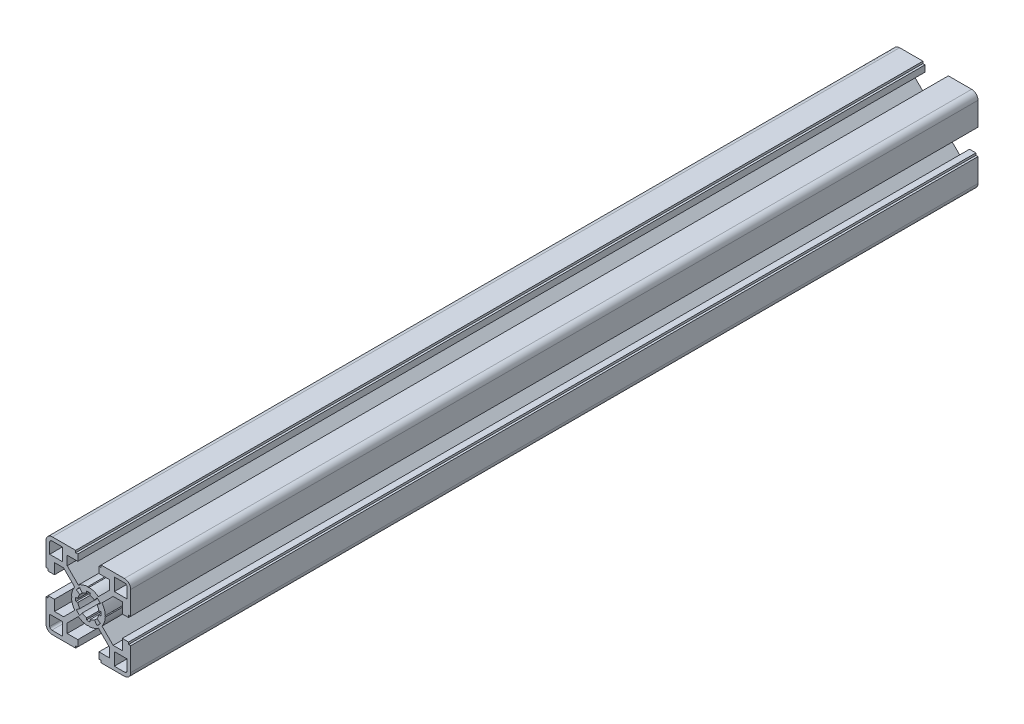
SolidWorks part; units mm, degrees
ref_plane "Plan de face" through (0, 0, 0) normal (0, 0, 1) x (1, 0, 0)
ref_plane "Plan de dessus" through (0, 0, 0) normal (0, 1, 0) x (1, 0, 0)
ref_plane "Plan de droite" through (0, 0, 0) normal (1, 0, 0) x (0, 0, -1)
ref_plane "Plan1" through (0, 0, 100) normal (0, 0, 1) x (1, 0, 0)
sketch "Esquisse1" plane through (0, 0, 100) normal (0, 0, 1) x (1, 0, 0)
  line L0 (18.25, 12.25) -> (12.25, 12.25)
  line L1 (12.25, 12.25) -> (12.25, 18.25)
  line L2 (12.25, 18.25) -> (17.25, 18.25)
  line L3 (18.25, 17.25) -> (18.25, 12.25)
  line L4 (-18.25, -12.25) -> (-12.25, -12.25)
  line L5 (-12.25, -12.25) -> (-12.25, -18.25)
  line L6 (-12.25, -18.25) -> (-17.25, -18.25)
  line L7 (-18.25, -17.25) -> (-18.25, -12.25)
  line L8 (6, -19) -> (6, -20)
  line L9 (6, -20) -> (17, -20)
  line L10 (20, -17) -> (20, -6)
  line L11 (20, -6) -> (19, -6)
  line L12 (19, -6) -> (19, -5)
  line L13 (19, -5) -> (16, -5)
  line L14 (16, -5) -> (16, -10)
  line L15 (16, -10) -> (11.6971, -10)
  line L16 (11.6971, -10) -> (6.4414, -4.7443)
  line L17 (7.9941, -0.3064) -> (7.7, 0)
  line L18 (7.7, 0) -> (7.9941, 0.3064)
  line L19 (6.4414, 4.7443) -> (11.6971, 10)
  line L20 (11.6971, 10) -> (16, 10)
  line L21 (16, 10) -> (16, 5)
  line L22 (16, 5) -> (19, 5)
  line L23 (19, 5) -> (19, 6)
  line L24 (19, 6) -> (20, 6)
  line L25 (20, 6) -> (20, 17)
  line L26 (17, 20) -> (6, 20)
  line L27 (6, 20) -> (6, 19)
  line L28 (6, 19) -> (5, 19)
  line L29 (5, 19) -> (5, 16)
  line L30 (5, 16) -> (10, 16)
  line L31 (10, 16) -> (10, 11.6971)
  line L32 (10, 11.6971) -> (4.7443, 6.4414)
  line L33 (0.3064, 7.9941) -> (0, 7.7)
  line L34 (0, 7.7) -> (-0.3064, 7.9941)
  line L35 (-4.7443, 6.4414) -> (-10, 11.6971)
  line L36 (-10, 11.6971) -> (-10, 16)
  line L37 (-10, 16) -> (-5, 16)
  line L38 (-5, 16) -> (-5, 19)
  line L39 (-5, 19) -> (-6, 19)
  line L40 (-6, 19) -> (-6, 20)
  line L41 (-6, 20) -> (-17, 20)
  line L42 (-20, 17) -> (-20, 6)
  line L43 (-20, 6) -> (-19, 6)
  line L44 (-19, 6) -> (-19, 5)
  line L45 (-19, 5) -> (-16, 5)
  line L46 (-16, 5) -> (-16, 10)
  line L47 (-16, 10) -> (-11.6971, 10)
  line L48 (-11.6971, 10) -> (-6.4414, 4.7443)
  line L49 (-7.9941, 0.3064) -> (-7.7, 0)
  line L50 (-7.7, 0) -> (-7.9941, -0.3064)
  line L51 (-6.4414, -4.7443) -> (-11.6971, -10)
  line L52 (-11.6971, -10) -> (-16, -10)
  line L53 (-16, -10) -> (-16, -5)
  line L54 (-16, -5) -> (-19, -5)
  line L55 (-19, -5) -> (-19, -6)
  line L56 (-19, -6) -> (-20, -6)
  line L57 (-20, -6) -> (-20, -17)
  line L58 (-17, -20) -> (-6, -20)
  line L59 (-6, -20) -> (-6, -19)
  line L60 (-6, -19) -> (-5, -19)
  line L61 (-5, -19) -> (-5, -16)
  line L62 (-5, -16) -> (-10, -16)
  line L63 (-10, -16) -> (-10, -11.6971)
  line L64 (-10, -11.6971) -> (-4.7443, -6.4414)
  line L65 (-0.3064, -7.9941) -> (0, -7.7)
  line L66 (0, -7.7) -> (0.3064, -7.9941)
  line L67 (4.7443, -6.4414) -> (10, -11.6971)
  line L68 (10, -11.6971) -> (10, -16)
  line L69 (10, -16) -> (5, -16)
  line L70 (5, -16) -> (5, -19)
  line L71 (5, -19) -> (6, -19)
  line L72 (-12.25, 18.25) -> (-12.25, 12.25)
  line L73 (-12.25, 12.25) -> (-18.25, 12.25)
  line L74 (-18.25, 12.25) -> (-18.25, 17.25)
  line L75 (-17.25, 18.25) -> (-12.25, 18.25)
  line L76 (12.25, -18.25) -> (12.25, -12.25)
  line L77 (12.25, -12.25) -> (18.25, -12.25)
  line L78 (18.25, -12.25) -> (18.25, -17.25)
  line L79 (17.25, -18.25) -> (12.25, -18.25)
  line L80 (-5.7057, -4.0552) -> (-4.0755, -2.8966)
  line L81 (-4.9435, -0.7494) -> (-5.9322, -0.8993)
  line L82 (-5.9322, 0.8993) -> (-4.9435, 0.7494)
  line L83 (-4.0755, 2.8966) -> (-5.7057, 4.0552)
  line L84 (-4.0641, 5.6994) -> (-2.903, 4.071)
  line L85 (-0.7494, 4.9435) -> (-0.8993, 5.9322)
  line L86 (0.8993, 5.9322) -> (0.7494, 4.9435)
  line L87 (2.903, 4.071) -> (4.0641, 5.6994)
  line L88 (5.7057, 4.0552) -> (4.0755, 2.8966)
  line L89 (4.9435, 0.7494) -> (5.9322, 0.8993)
  line L90 (5.9322, -0.8993) -> (4.9435, -0.7494)
  line L91 (4.0755, -2.8966) -> (5.7057, -4.0552)
  line L92 (4.0641, -5.6994) -> (2.903, -4.071)
  line L93 (0.7494, -4.9435) -> (0.8993, -5.9322)
  line L94 (-0.8993, -5.9322) -> (-0.7494, -4.9435)
  line L95 (-2.903, -4.071) -> (-4.0641, -5.6994)
  arc A0 (17.25, 18.25) -> (18.25, 17.25) centre (17.25, 17.25) cw
  arc A1 (-17.25, -18.25) -> (-18.25, -17.25) centre (-17.25, -17.25) cw
  arc A2 (17, -20) -> (20, -17) centre (17, -17) ccw
  arc A3 (6.4414, -4.7443) -> (7.9941, -0.3064) centre (0, 0) ccw
  arc A4 (7.9941, 0.3064) -> (6.4414, 4.7443) centre (0, 0) ccw
  arc A5 (20, 17) -> (17, 20) centre (17, 17) ccw
  arc A6 (4.7443, 6.4414) -> (0.3064, 7.9941) centre (0, 0) ccw
  arc A7 (-0.3064, 7.9941) -> (-4.7443, 6.4414) centre (0, 0) ccw
  arc A8 (-17, 20) -> (-20, 17) centre (-17, 17) ccw
  arc A9 (-6.4414, 4.7443) -> (-7.9941, 0.3064) centre (0, 0) ccw
  arc A10 (-7.9941, -0.3064) -> (-6.4414, -4.7443) centre (0, 0) ccw
  arc A11 (-20, -17) -> (-17, -20) centre (-17, -17) ccw
  arc A12 (-4.7443, -6.4414) -> (-0.3064, -7.9941) centre (0, 0) ccw
  arc A13 (0.3064, -7.9941) -> (4.7443, -6.4414) centre (0, 0) ccw
  arc A14 (-18.25, 17.25) -> (-17.25, 18.25) centre (-17.25, 17.25) cw
  arc A15 (18.25, -17.25) -> (17.25, -18.25) centre (17.25, -17.25) cw
  arc A16 (-4.0641, -5.6994) -> (-5.7057, -4.0552) centre (0, 0) cw
  arc A17 (-4.0755, -2.8966) -> (-4.9435, -0.7494) centre (0, 0) cw
  arc A18 (-5.9322, -0.8993) -> (-5.9322, 0.8993) centre (0, 0) cw
  arc A19 (-4.9435, 0.7494) -> (-4.0755, 2.8966) centre (0, 0) cw
  arc A20 (-5.7057, 4.0552) -> (-4.0641, 5.6994) centre (0, 0) cw
  arc A21 (-2.903, 4.071) -> (-0.7494, 4.9435) centre (0, 0) cw
  arc A22 (-0.8993, 5.9322) -> (0.8993, 5.9322) centre (0, 0) cw
  arc A23 (0.7494, 4.9435) -> (2.903, 4.071) centre (0, 0) cw
  arc A24 (4.0641, 5.6994) -> (5.7057, 4.0552) centre (0, 0) cw
  arc A25 (4.0755, 2.8966) -> (4.9435, 0.7494) centre (0, 0) cw
  arc A26 (5.9322, 0.8993) -> (5.9322, -0.8993) centre (0, 0) cw
  arc A27 (4.9435, -0.7494) -> (4.0755, -2.8966) centre (0, 0) cw
  arc A28 (5.7057, -4.0552) -> (4.0641, -5.6994) centre (0, 0) cw
  arc A29 (2.903, -4.071) -> (0.7494, -4.9435) centre (0, 0) cw
  arc A30 (0.8993, -5.9322) -> (-0.8993, -5.9322) centre (0, 0) cw
  arc A31 (-0.7494, -4.9435) -> (-2.903, -4.071) centre (0, 0) cw
extrude "Boss.-Extru.1" add sketch "Esquisse1" against normal blind 400
